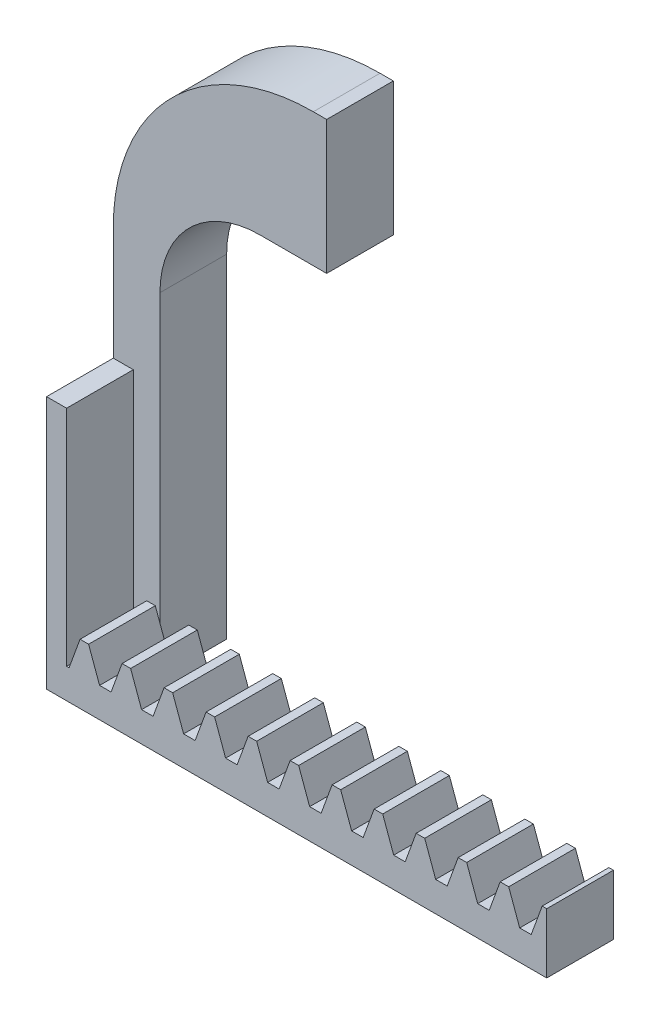
SolidWorks part; units mm, degrees
ref_plane "Ebene vorne" through (0, 0, 0) normal (0, 0, 1) x (1, 0, 0)
ref_plane "Ebene oben" through (0, 0, 0) normal (0, 1, 0) x (1, 0, 0)
ref_plane "Ebene rechts" through (0, 0, 0) normal (1, 0, 0) x (0, 0, -1)
sketch "Sketch1" plane through (0, 0, 0) normal (0, 0, 1) x (1, 0, 0)
  line L1 (7, 0) -> (0, 0)
  line L4 (0, 0) -> (0, 47.7)
  line L6 (7, 50) -> (7, 0)
  line L7 (32, 85) -> (32, 65)
  line L8 (32, 65) -> (22, 65)
  line L9 (32, 85) -> (30, 85)
  line L10 (0, 47.7) -> (0, 55)
  arc A0 (22, 65) -> (7, 50) centre (22, 50) ccw
  arc A2 (30, 85) -> (0, 55) centre (30, 55) ccw
  dimension "D6" = 30
  dimension "D8" = 30
  dimension "D1" = 20
  dimension "D2" = 85
  dimension "D3" = 47.7
  dimension "D4" = 7
  dimension "D5" = 32
  dimension "D7" = 50
  dimension "D9" = 10
extrude "Boss-Extrude1" add sketch "Sketch1" along normal blind 10
sketch "Skizze2" plane through (0, 0, 10) normal (0, 0, 1) x (1, 0, 0)
  line L1 (0, 0) -> (75, 0)
  line L2 (0, 0) -> (0, 9)
  line L3 (0, 9) -> (75, 9)
  line L4 (75, 0) -> (75, 9)
  dimension "D1" = 75
  dimension "D2" = 9
extrude "Aufsatz-Linear austragen1" add sketch "Skizze2" along normal blind 10
sketch "Skizze3" plane through (0, 0, 20) normal (0, 0, 1) x (1, 0, 0)
  line L168 (3.3709, 4.4746) -> (1.6471, 4.4746)
  line L169 (5.018, 9) -> (3.3709, 4.4746)
  line L170 (2.509, 20.5224) -> (2.509, 56.5269) construction
  line L171 (5.018, 9) -> (0, 9)
  line L172 (0, 9) -> (1.6471, 4.4746)
  line L173 (1.6904, 4.3556) -> (3.3275, 4.3556) construction
  line L174 (3.3275, 4.3556) -> (3.3275, 56.5269) construction
  line L175 (1.6904, 4.3556) -> (1.6904, 49.8226) construction
  line L220 (9.6709, 4.4746) -> (7.9471, 4.4746)
  line L221 (6.3, 9) -> (7.9471, 4.4746)
  line L222 (11.318, 9) -> (6.3, 9)
  line L223 (11.318, 9) -> (9.6709, 4.4746)
  line L224 (15.9709, 4.4746) -> (14.2471, 4.4746)
  line L225 (12.6, 9) -> (14.2471, 4.4746)
  line L226 (17.618, 9) -> (12.6, 9)
  line L227 (17.618, 9) -> (15.9709, 4.4746)
  line L228 (22.2709, 4.4746) -> (20.5471, 4.4746)
  line L229 (18.9, 9) -> (20.5471, 4.4746)
  line L230 (23.918, 9) -> (18.9, 9)
  line L231 (23.918, 9) -> (22.2709, 4.4746)
  line L232 (28.5709, 4.4746) -> (26.8471, 4.4746)
  line L233 (25.2, 9) -> (26.8471, 4.4746)
  line L234 (30.218, 9) -> (25.2, 9)
  line L235 (30.218, 9) -> (28.5709, 4.4746)
  line L236 (34.8709, 4.4746) -> (33.1471, 4.4746)
  line L237 (31.5, 9) -> (33.1471, 4.4746)
  line L238 (36.518, 9) -> (31.5, 9)
  line L239 (36.518, 9) -> (34.8709, 4.4746)
  line L240 (41.1709, 4.4746) -> (39.4471, 4.4746)
  line L241 (37.8, 9) -> (39.4471, 4.4746)
  line L242 (42.818, 9) -> (37.8, 9)
  line L243 (42.818, 9) -> (41.1709, 4.4746)
  line L244 (47.4709, 4.4746) -> (45.7471, 4.4746)
  line L245 (44.1, 9) -> (45.7471, 4.4746)
  line L246 (49.118, 9) -> (44.1, 9)
  line L247 (49.118, 9) -> (47.4709, 4.4746)
  line L248 (53.7709, 4.4746) -> (52.0471, 4.4746)
  line L249 (50.4, 9) -> (52.0471, 4.4746)
  line L250 (55.418, 9) -> (50.4, 9)
  line L251 (55.418, 9) -> (53.7709, 4.4746)
  line L252 (60.0709, 4.4746) -> (58.3471, 4.4746)
  line L253 (56.7, 9) -> (58.3471, 4.4746)
  line L254 (61.718, 9) -> (56.7, 9)
  line L255 (61.718, 9) -> (60.0709, 4.4746)
  line L256 (66.3709, 4.4746) -> (64.6471, 4.4746)
  line L257 (63, 9) -> (64.6471, 4.4746)
  line L258 (68.018, 9) -> (63, 9)
  line L259 (68.018, 9) -> (66.3709, 4.4746)
  line L260 (72.6709, 4.4746) -> (70.9471, 4.4746)
  line L261 (69.3, 9) -> (70.9471, 4.4746)
  line L262 (74.318, 9) -> (69.3, 9)
  line L263 (74.318, 9) -> (72.6709, 4.4746)
  dimension "D1" = 5.018
  dimension "D2" = 1.7237
  dimension "D3" = 4.5254
extrude "Schnitt-Linear austragen2" cut sketch "Skizze3" against normal blind 10
sketch "Skizze4" plane through (0, 0, 0) normal (-1, 0, 0) x (0, 0, 1)
  line L0 (0, 55) -> (0, 0) construction
  line L1 (20, 0) -> (0, 0)
  line L2 (20, 0) -> (20, 38)
  line L3 (10, 48) -> (0, 48)
  line L4 (0, 0) -> (0, 48)
  line L5 (10, 55) -> (10, 9) construction
  line L7 (10, 48) -> (10, 38)
  line L8 (10, 38) -> (20, 38)
  dimension "D1" = 48
  dimension "D2" = 10
extrude "Aufsatz-Linear austragen2" add sketch "Skizze4" against normal blind 3
